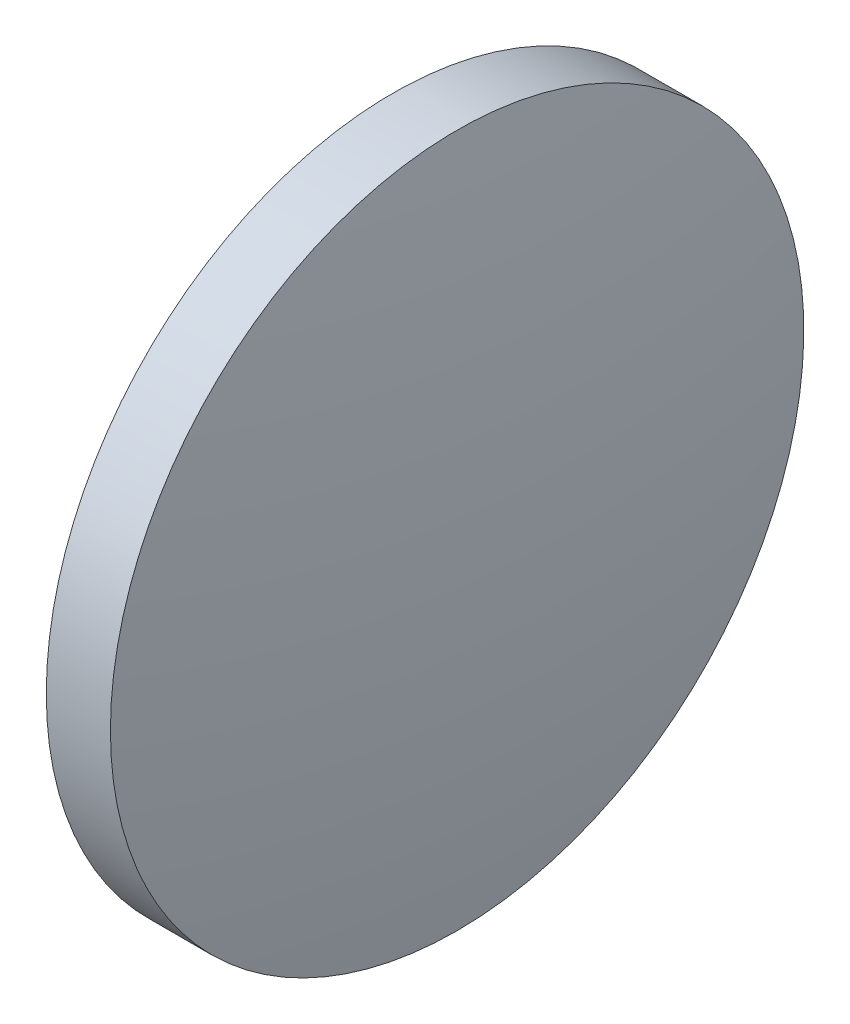
SolidWorks part; units mm, degrees
ref_plane "前视基准面" through (0, 0, 0) normal (0, 0, 1) x (1, 0, 0)
ref_plane "上视基准面" through (0, 0, 0) normal (0, 1, 0) x (1, 0, 0)
ref_plane "右视基准面" through (0, 0, 0) normal (1, 0, 0) x (0, 0, -1)
sketch "草图1" plane through (0, 0, 0) normal (0, 0, 1) x (1, 0, 0)
  line L0 (427.2353, 100.3117) -> (437.9919, 100.3117) construction
  line L1 (430.9606, 100.3117) -> (430.9606, 108.3117)
  line L2 (433.0606, 100.3117) -> (430.9606, 100.3117)
  line L5 (430.9606, 108.3117) -> (432.4406, 108.3117)
  arc A0 (433.0606, 100.3117) -> (432.4406, 108.3117) centre (381.1377, 100.3117) ccw
revolve "旋转1" add sketch "草图1" angle 360 about L0
